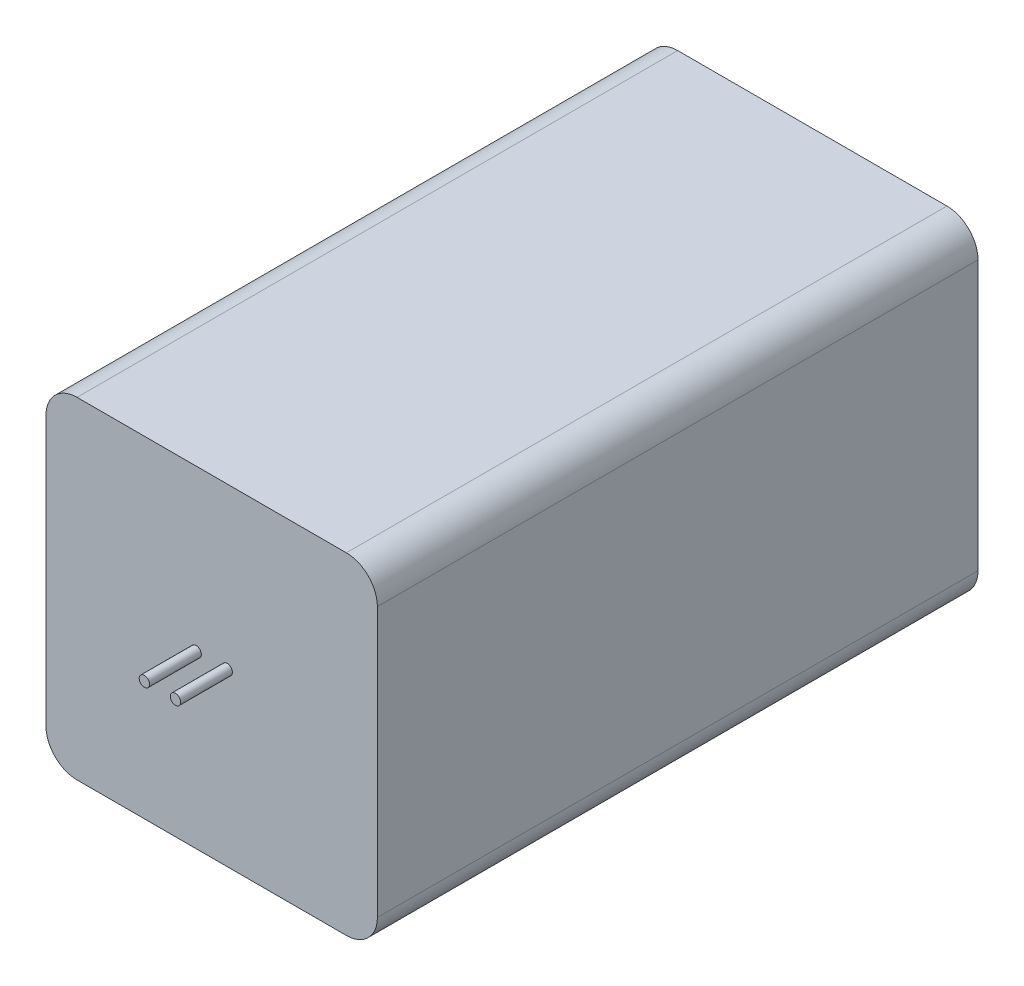
SolidWorks part; units mm, degrees
ref_plane "正面" through (0, 0, 0) normal (0, 0, 1) x (1, 0, 0)
ref_plane "平面" through (0, 0, 0) normal (0, 1, 0) x (1, 0, 0)
ref_plane "右側面" through (0, 0, 0) normal (1, 0, 0) x (0, 0, -1)
sketch "ｽｹｯﾁ1" plane through (0, 0, 0) normal (0, 0, 1) x (1, 0, 0)
  line L1 (16, 16) -> (-16, 16)
  line L2 (16, 16) -> (16, -16)
  line L3 (16, -16) -> (-16, -16)
  line L4 (-16, 16) -> (-16, -16)
  line L5 (16, 16) -> (-16, -16) construction
  line L6 (16, -16) -> (-16, 16) construction
  point P0 (0, 0)
  dimension "D1" = 32
  dimension "D2" = 32
extrude "ﾎﾞｽ - 押し出し1" add sketch "ｽｹｯﾁ1" along normal blind 58
fillet "ﾌｨﾚｯﾄ1" radius 3 4 edges at (16, -16, 29) (-16, -16, 29) (-16, 16, 29) (16, 16, 29)
sketch "ｽｹｯﾁ2" plane through (0, 0, 58) normal (0, 0, 1) x (1, 0, 0)
  line L0 (-16, 0) -> (16, 0) construction
  line L1 (-16, 13) -> (-16, -13) construction
  line L2 (16, -13) -> (16, 13) construction
  circle A0 centre (-1.5, 0.5) radius 0.5
  circle A1 centre (1.5, 0.5) radius 0.5
  dimension "D1" = 1
  dimension "D2" = 1.5
  dimension "D3" = 1.5
extrude "ﾎﾞｽ - 押し出し2" add sketch "ｽｹｯﾁ2" along normal blind 5 separate body
equation "\"D3@ｽｹｯﾁ2\"=\"D2@ｽｹｯﾁ2\""
